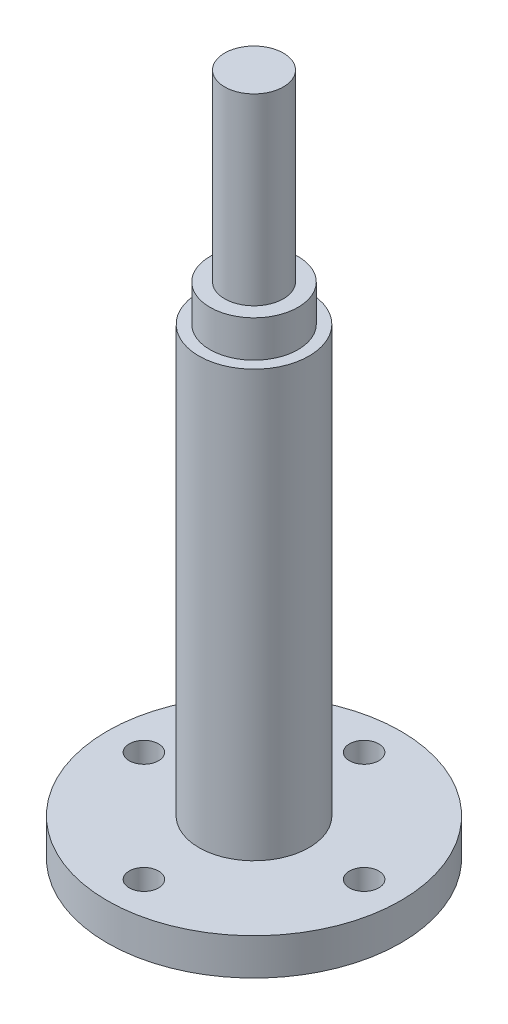
SolidWorks part; units mm, degrees
ref_plane "Front Plane" through (0, 0, 0) normal (0, 0, 1) x (1, 0, 0)
ref_plane "Top Plane" through (0, 0, 0) normal (0, 1, 0) x (1, 0, 0)
ref_plane "Right Plane" through (0, 0, 0) normal (1, 0, 0) x (0, 0, -1)
sketch "Sketch1" plane through (0, 0, 0) normal (0, 1, 0) x (1, 0, 0)
  circle A0 centre (0, 0) radius 20
  dimension "D1" = 40
extrude "Boss-Extrude1" add sketch "Sketch1" along normal blind 5
sketch "Sketch2" plane through (0, 5, 0) normal (0, 1, 0) x (1, 0, 0)
  circle A0 centre (0, 0) radius 7.5
  dimension "D1" = 15
extrude "Boss-Extrude2" add sketch "Sketch2" along normal blind 63
sketch "Sketch3" plane through (0, 68, 0) normal (0, 1, 0) x (1, 0, 0)
  circle A0 centre (0, 0) radius 4
  dimension "D1" = 8
extrude "Boss-Extrude3" add sketch "Sketch3" along normal blind 25
sketch "Sketch4" plane through (0, 5, 0) normal (0, 1, 0) x (1, 0, 0)
  circle A0 centre (0, 0) radius 15 construction
  circle A1 centre (0, 15) radius 2
  circle A2 centre (15, 0) radius 2
  circle A3 centre (0, -15) radius 2
  circle A4 centre (-15, 0) radius 2
  point P14 (0, 0)
  dimension "D1" = 30
  dimension "D2" = 4
  dimension "D3" = 4
extrude "Cut-Extrude1" cut sketch "Sketch4" against normal blind 25
sketch "Sketch5" plane through (0, 68, 0) normal (0, 1, 0) x (1, 0, 0)
  circle A0 centre (0, 0) radius 6
  circle A1 centre (0, 0) radius 7.5
  circle A2 centre (0, 0) radius 7.5 construction
  dimension "D1" = 12
extrude "Cut-Extrude2" cut sketch "Sketch5" against normal blind 5
